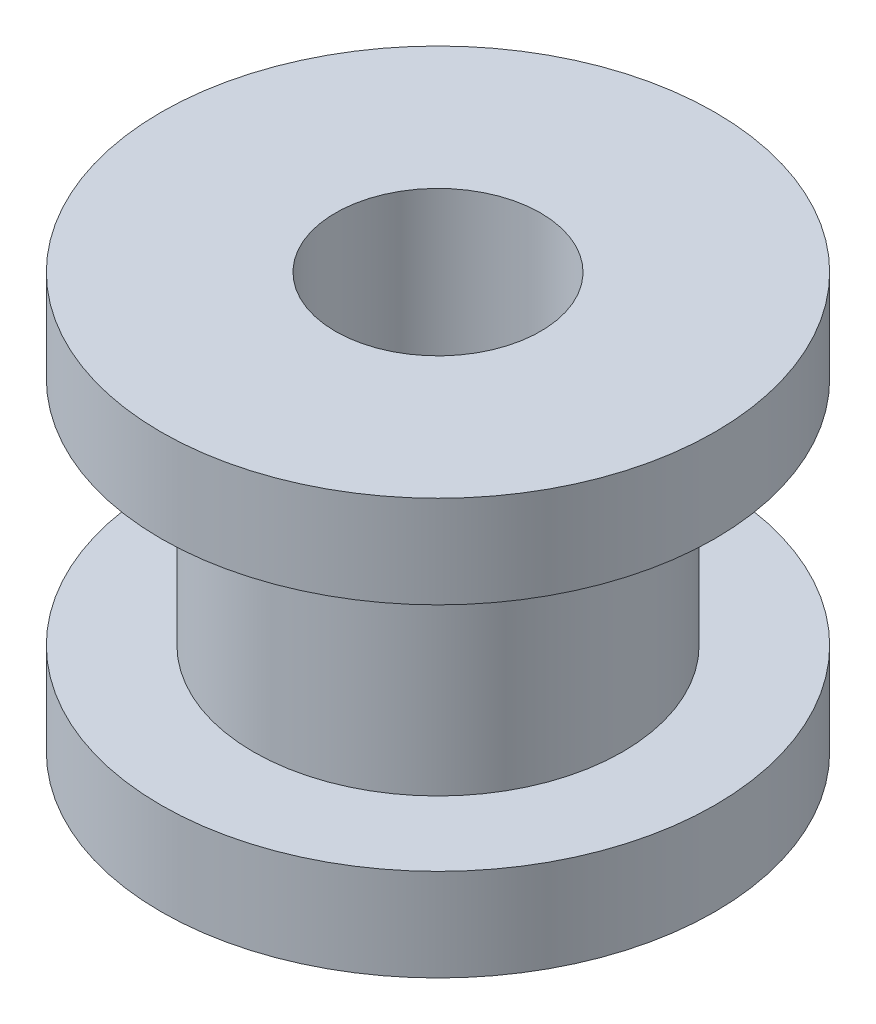
SolidWorks part; units mm, degrees
ref_plane "Front Plane" through (0, 0, 0) normal (0, 0, 1) x (1, 0, 0)
ref_plane "Top Plane" through (0, 0, 0) normal (0, 1, 0) x (1, 0, 0)
ref_plane "Right Plane" through (0, 0, 0) normal (1, 0, 0) x (0, 0, -1)
sketch "Sketch1" plane through (0, 0, 0) normal (0, 1, 0) x (1, 0, 0)
  circle A0 centre (0, 0) radius 4
  dimension "D1" = 8
extrude "Boss-Extrude1" add sketch "Sketch1" along normal blind 5
sketch "Sketch2" plane through (0, 5, 0) normal (0, 1, 0) x (1, 0, 0)
  circle A0 centre (0, 0) radius 6
  dimension "D1" = 12
extrude "Boss-Extrude2" add sketch "Sketch2" along normal blind 2
ref_plane "Plane1" through (0, 2.5, 0) normal (0, -1, 0) x (-1, 0, 0)
mirror "Mirror1" about plane through (0, 2.5, 0) normal (0, -1, 0) of "Boss-Extrude2"
sketch "Sketch3" plane through (0, 7, 0) normal (0, 1, 0) x (1, 0, 0)
  circle A0 centre (0, 0) radius 2.2225
  dimension "D1" = 4.445
extrude "Cut-Extrude1" cut sketch "Sketch3" against normal through all
